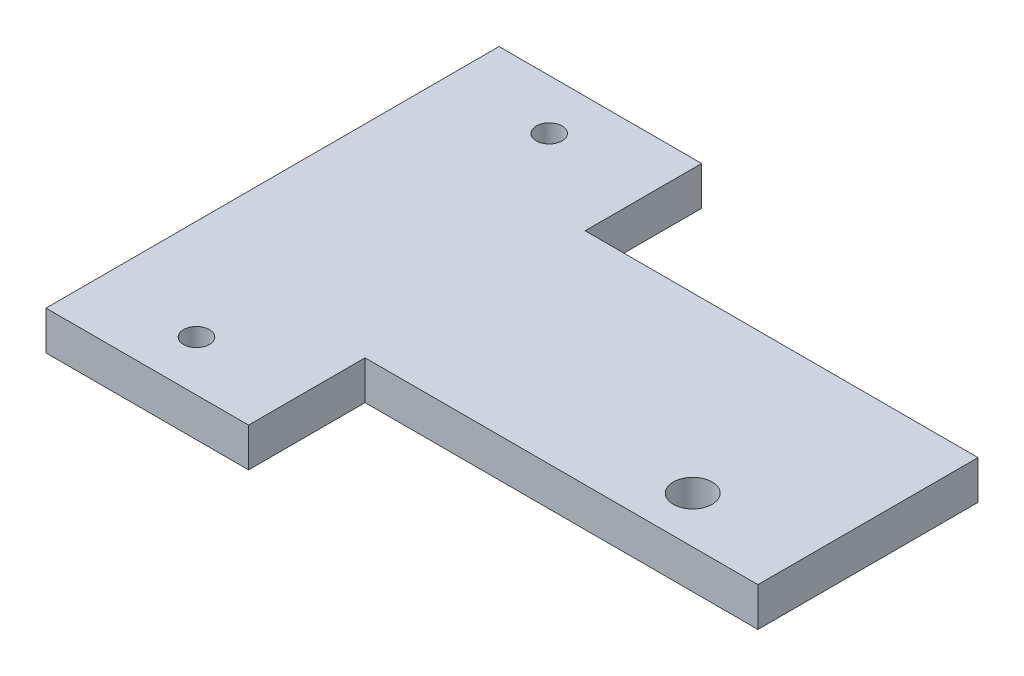
SolidWorks part; units mm, degrees
ref_plane "Front Plane" through (0, 0, 0) normal (0, 0, 1) x (1, 0, 0)
ref_plane "Top Plane" through (0, 0, 0) normal (0, 1, 0) x (1, 0, 0)
ref_plane "Right Plane" through (0, 0, 0) normal (1, 0, 0) x (0, 0, -1)
sketch "Sketch1" plane through (0, 0, 0) normal (0, 1, 0) x (1, 0, 0)
  line L1 (23, -8.5) -> (-23, -8.5)
  line L2 (23, -8.5) -> (23, 8.5)
  line L3 (23, 8.5) -> (-23, 8.5)
  line L4 (-23, -8.5) -> (-23, 8.5)
  line L5 (23, -8.5) -> (-23, 8.5) construction
  line L6 (23, 8.5) -> (-23, -8.5) construction
  point P0 (0, 0)
  dimension "D1" = 17
  dimension "D2" = 46
extrude "Boss-Extrude1" add sketch "Sketch1" along normal blind 3
sketch "Sketch2" plane through (0, 0, -8.5) normal (0, 0, -1) x (-1, 0, 0)
  line L0 (-23, 3) -> (23, 3) construction
  line L1 (23, 0) -> (7.35, 0)
  line L2 (23, 0) -> (23, 3)
  line L3 (23, 3) -> (7.35, 3)
  line L4 (7.35, 0) -> (7.35, 3)
  dimension "D1" = 15.65
extrude "Boss-Extrude2" add sketch "Sketch2" along normal blind 9
mirror "Mirror1" about plane through (0, 0, 0) normal (0, 0, 1) of "Boss-Extrude2"
sketch "Sketch3" plane through (0, 3, 0) normal (0, 1, 0) x (1, 0, 0)
  circle A0 centre (-15.25, 13.625) radius 1
  circle A1 centre (-15.25, -13.625) radius 1
  dimension "D1" = 2
extrude "Cut-Extrude1" cut sketch "Sketch3" against normal blind 10
sketch "Sketch4" plane through (0, 3, 0) normal (0, 1, 0) x (1, 0, 0)
  line L0 (-7.35, -8.5) -> (23, -8.5) construction
  line L2 (-23, 17.5) -> (-23, -17.5) construction
  circle A0 centre (14.36, -4.9) radius 1.5
  dimension "D1" = 3.6
  dimension "D2" = 3
  dimension "D3" = 37.36
extrude "Cut-Extrude2" cut sketch "Sketch4" against normal blind 10
